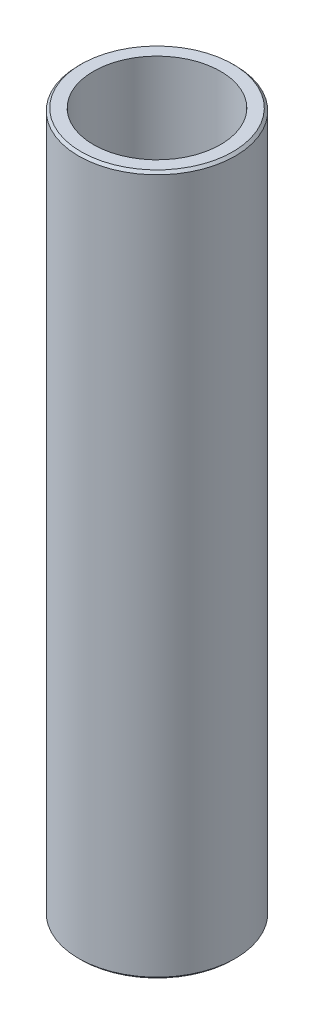
SolidWorks part; units mm, degrees
ref_plane "Front Plane" through (0, 0, 0) normal (0, 0, 1) x (1, 0, 0)
ref_plane "Top Plane" through (0, 0, 0) normal (0, 1, 0) x (1, 0, 0)
ref_plane "Right Plane" through (0, 0, 0) normal (1, 0, 0) x (0, 0, -1)
sketch "Sketch1" plane through (0, 0, 0) normal (0, 1, 0) x (1, 0, 0)
  circle A0 centre (0, 0) radius 7.94
  circle A1 centre (0, 0) radius 6.44
  dimension "D1" = 15.88
  dimension "D2" = 1.5
extrude "Boss-Extrude1" add sketch "Sketch1" along normal blind 70.91
chamfer "Chamfer1" distance 0.25 angle 45 2 edges at (0, 0, 7.94) (0, 70.91, 7.94)
